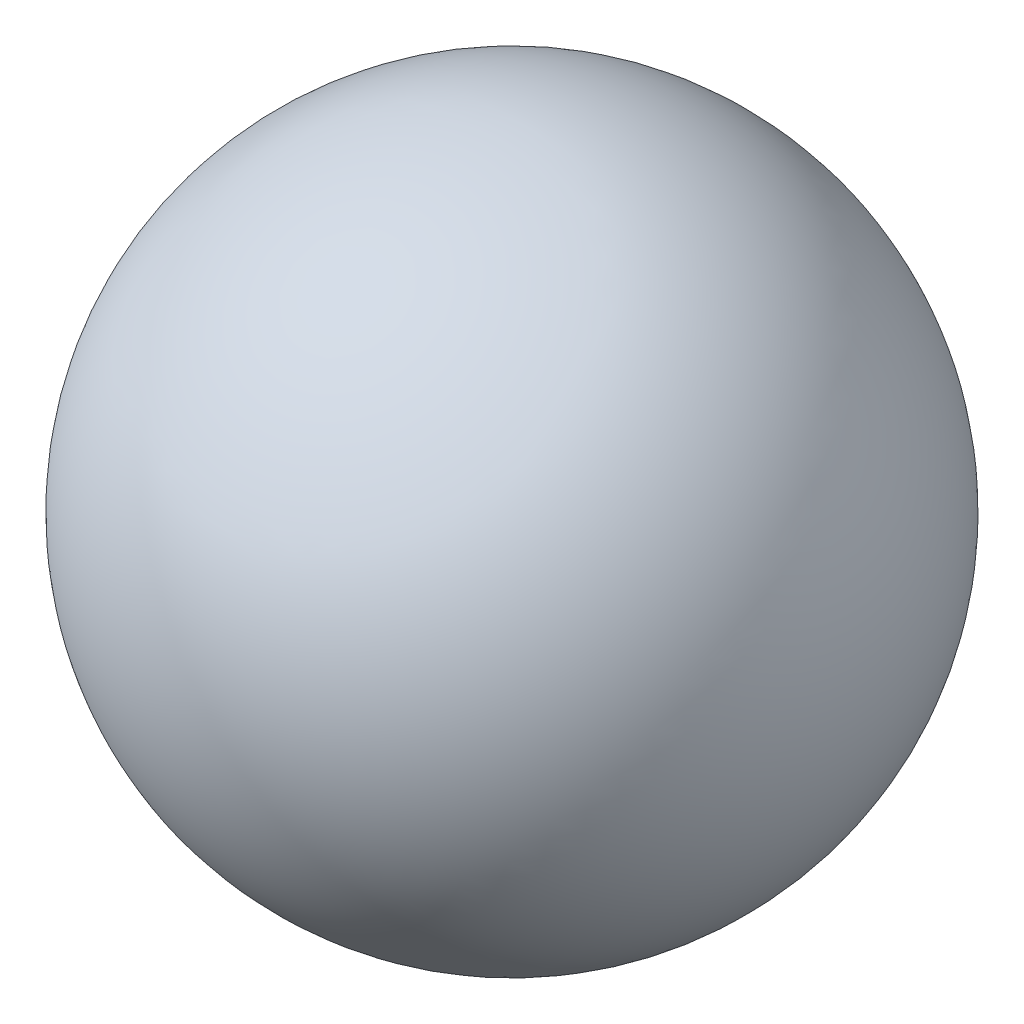
SolidWorks part; units mm, degrees
ref_plane "Front Plane" through (0, 0, 0) normal (0, 0, 1) x (1, 0, 0)
ref_plane "Top Plane" through (0, 0, 0) normal (0, 1, 0) x (1, 0, 0)
ref_plane "Right Plane" through (0, 0, 0) normal (1, 0, 0) x (0, 0, -1)
sketch "Sketch1" plane through (0, 0, 0) normal (1, 0, 0) x (0, 0, -1)
  line L0 (-20, 0) -> (20, 0)
  circle A0 centre (0, 0) radius 20
  dimension "D1" = 40
revolve "Revolve1" add sketch "Sketch1" angle 360 about L0
